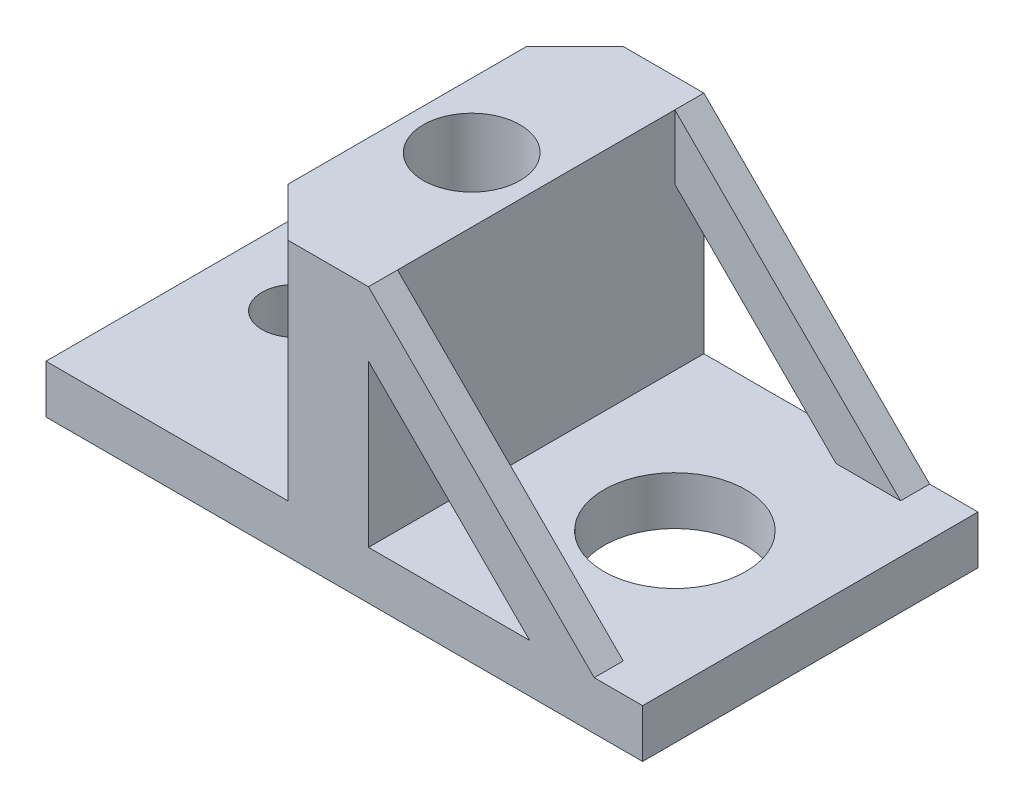
SolidWorks part; units mm, degrees
ref_plane "Front Plane" through (0, 0, 0) normal (0, 0, 1) x (1, 0, 0)
ref_plane "Top Plane" through (0, 0, 0) normal (0, 1, 0) x (1, 0, 0)
ref_plane "Right Plane" through (0, 0, 0) normal (1, 0, 0) x (0, 0, -1)
sketch "Sketch1" plane through (0, 0, 0) normal (0, 1, 0) x (1, 0, 0)
  line L0 (0, 26) -> (92.5, 26) construction
  line L1 (0, 0) -> (92.5, 0)
  line L2 (0, 0) -> (0, 52)
  line L3 (0, 52) -> (92.5, 52)
  line L4 (92.5, 0) -> (92.5, 52)
  circle A0 centre (12.5, 26) radius 5.015
  circle A1 centre (40, 26) radius 7.5
  circle A2 centre (71.5, 26) radius 11
  point P11 (74.6581, 21)
  point P12 (0, 0)
  dimension "D3" = 10.03
  dimension "D4" = 15
  dimension "D7" = 22
  dimension "D8" = 31.5
  dimension "D1" = 92.5
  dimension "D2" = 52
  dimension "D5" = 27.5
  dimension "D6" = 12.5
extrude "Boss-Extrude1" add sketch "Sketch1" along normal blind 7.5
sketch "Sketch2" plane through (0, 7.5, 0) normal (0, 1, 0) x (1, 0, 0)
  line L0 (0, 0) -> (92.5, 0) construction
  line L1 (30, 0) -> (50, 0)
  line L2 (30, 0) -> (30, 52)
  line L3 (30, 52) -> (50, 52)
  line L4 (50, 0) -> (50, 52)
  line L5 (92.5, 52) -> (0, 52) construction
  line L6 (30, 7.5) -> (37.5, 0)
  line L7 (30, 44.5) -> (37.5, 52)
  circle A0 centre (40, 26) radius 7.5
  point P11 (40, 0)
  line M9 (92.5, 52) -> (0, 52)
  circle M11 centre (40, 26) radius 7.5
  dimension "D1" = 15
  dimension "D2" = 20
  dimension "D3" = 7.5
  dimension "D4" = 7.5
  dimension "D5" = 7.5
  dimension "D6" = 7.5
extrude "Boss-Extrude2" add sketch "Sketch2" along normal blind 35 contours L7 L2 L6 L1 L4 M9 M11
sketch "Sketch3" plane through (0, 0, 0) normal (0, 0, 1) x (1, 0, 0)
  line L0 (50, 42.5) -> (85, 7.5)
  line L1 (50, 7.5) -> (92.5, 7.5) construction
  line L2 (85, 7.5) -> (75, 7.5)
  line L3 (75, 7.5) -> (50, 32.5)
  line L4 (50, 42.5) -> (50, 7.5) construction
  line L5 (50, 32.5) -> (50, 42.5)
  point P5 (81.8356, 7.5)
  dimension "D1" = 35
  dimension "D2" = 25
extrude "Boss-Extrude3" add sketch "Sketch3" against normal blind 4.5
sketch "Sketch4" plane through (0, 0, -52) normal (0, 0, -1) x (-1, 0, 0)
  line L0 (-50, 42.5) -> (-85, 7.5)
  line L1 (-92.5, 7.5) -> (-50, 7.5) construction
  line L2 (-85, 7.5) -> (-75, 7.5)
  line L3 (-75, 7.5) -> (-50, 32.5)
  line L4 (-50, 42.5) -> (-50, 7.5) construction
  line L5 (-50, 32.5) -> (-50, 42.5)
  dimension "D1" = 25
  dimension "D2" = 35
extrude "Boss-Extrude4" add sketch "Sketch4" against normal blind 4.5
